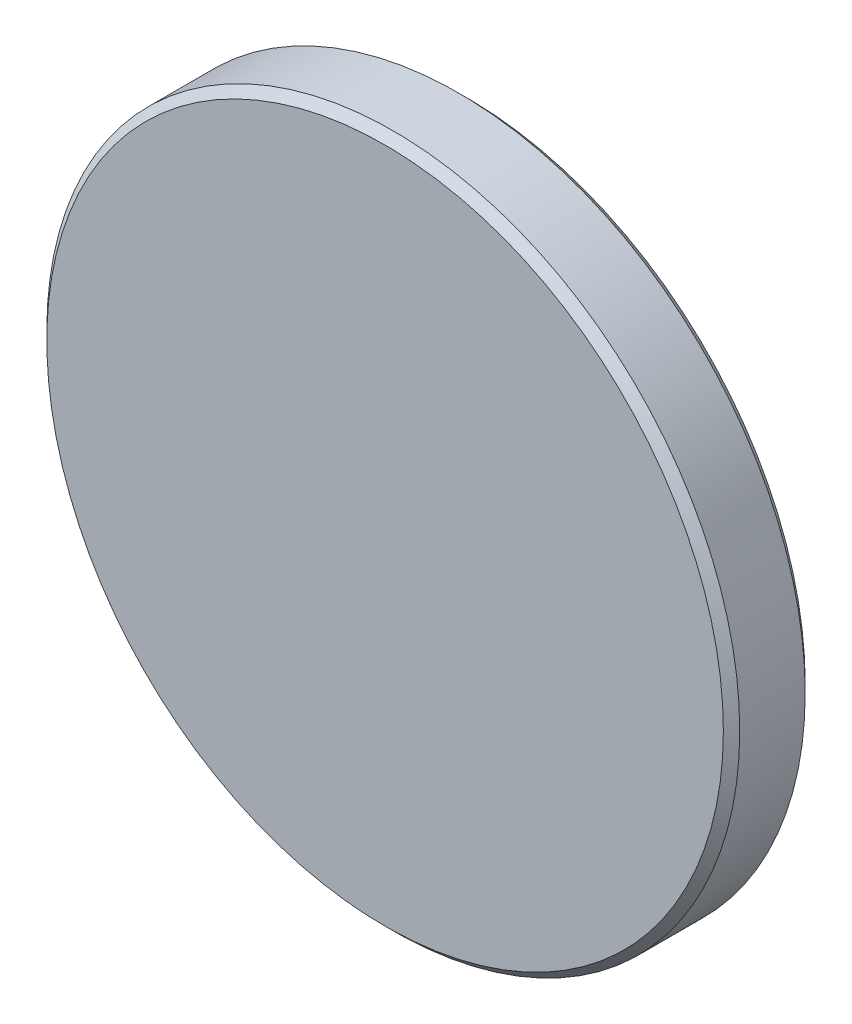
SolidWorks part; units mm, degrees
ref_plane "前视基准面" through (0, 0, 0) normal (0, 0, 1) x (1, 0, 0)
ref_plane "上视基准面" through (0, 0, 0) normal (0, 1, 0) x (1, 0, 0)
ref_plane "右视基准面" through (0, 0, 0) normal (1, 0, 0) x (0, 0, -1)
sketch "草图1" plane through (0, 0, 0) normal (0, 0, 1) x (1, 0, 0)
  circle A0 centre (0, 0) radius 12.7
  dimension "D1" = 25.4
extrude "凸台-拉伸1" add sketch "草图1" along normal blind 3
chamfer "倒角1" distance 0.3 angle 45 2 edges at (12.7, 0, 0) (12.7, 0, 3)
